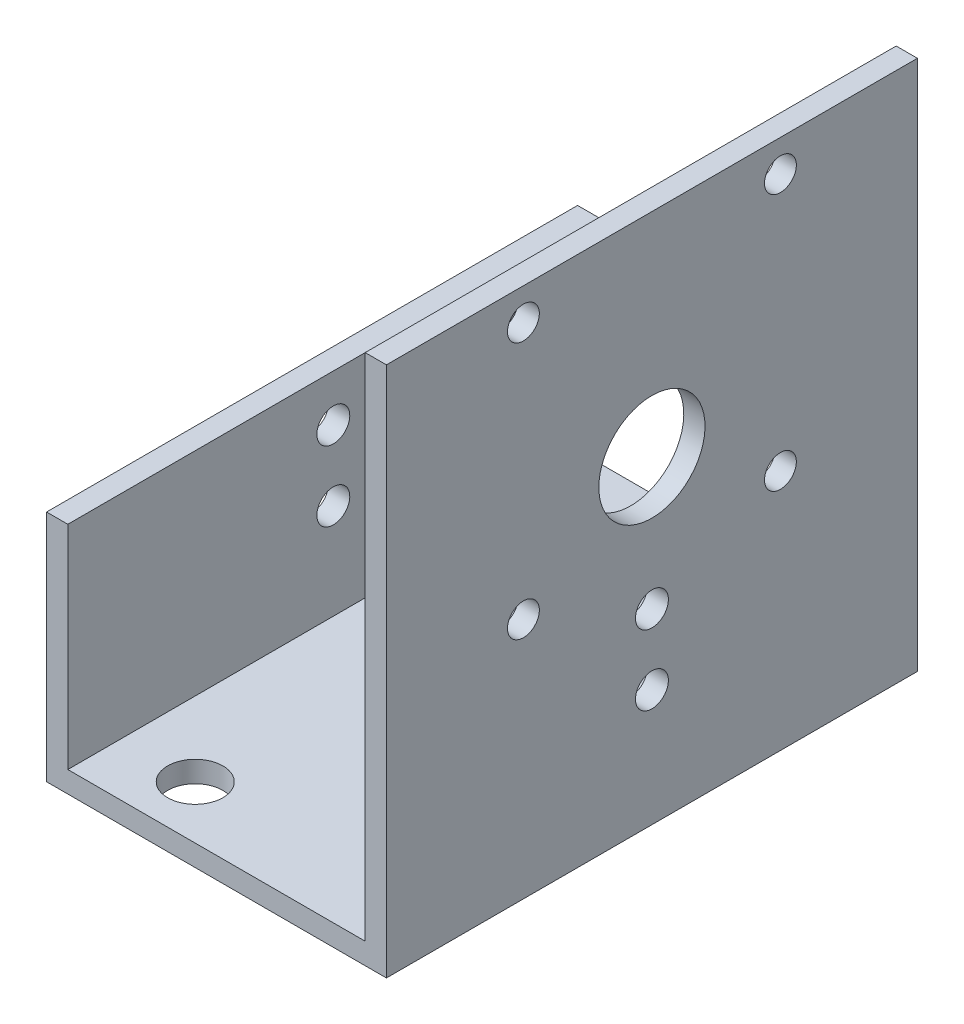
SolidWorks part; units mm, degrees
ref_plane "Plan de face" through (0, 0, 0) normal (0, 0, 1) x (1, 0, 0)
ref_plane "Plan de dessus" through (0, 0, 0) normal (0, 1, 0) x (1, 0, 0)
ref_plane "Plan de droite" through (0, 0, 0) normal (1, 0, 0) x (0, 0, -1)
sketch "Esquisse1" plane through (0, 0, 0) normal (0, 0, 1) x (1, 0, 0)
  line L0 (-28, -48) -> (-28, -50) construction
  line L1 (0, 0) -> (2, 0)
  line L2 (0, 0) -> (0, -48)
  line L4 (2, 0) -> (2, -50)
  line L5 (0, -48) -> (-28, -48)
  line L7 (2, -50) -> (-28, -50)
  line L9 (-28, -50) -> (-30, -50)
  line L10 (-28, -48) -> (-28, -28)
  line L11 (-28, -28) -> (-30, -28)
  line L12 (-30, -50) -> (-30, -28)
  dimension "D1" = 50
  dimension "D2" = 2
  dimension "D3" = 22
  dimension "D4" = 30
extrude "Extrusion1" add sketch "Esquisse1" along normal mid plane 50
sketch "Esquisse2" plane through (2, 0, 0) normal (1, 0, 0) x (0, 0, -1)
  line L0 (0, 0) -> (0, -20) construction
  line L1 (-25, 0) -> (25, 0) construction
  line L2 (-12.1, -3) -> (12.1, -3) construction
  line L3 (-12.1, -3) -> (-12.1, -27.2) construction
  line L4 (-12.1, -27.2) -> (12.1, -27.2) construction
  line L5 (12.1, -3) -> (12.1, -27.2) construction
  circle A0 centre (-12.1, -3) radius 1.5
  circle A1 centre (-12.1, -27.2) radius 1.5
  circle A2 centre (12.1, -27.2) radius 1.5
  circle A3 centre (12.1, -3) radius 1.5
  circle A4 centre (0, -20) radius 5
  dimension "D1" = 3
  dimension "D2" = 10
  dimension "D7" = 7.2
  dimension "D3" = 3
  dimension "D4" = 24.2
  dimension "D5" = 12.1
  dimension "D6" = 24.2
extrude "Enlèv. mat.-Extru.1" cut sketch "Esquisse2" against normal blind 10
sketch "Esquisse3" plane through (2, 0, 0) normal (1, 0, 0) x (0, 0, -1)
  line L0 (0, -50) -> (0, -39) construction
  line L1 (-25, -50) -> (25, -50) construction
  line L2 (0, -39) -> (0, -32.4) construction
  circle A0 centre (0, -32.4) radius 1.55
  circle A1 centre (0, -39) radius 1.55
  dimension "D2" = 3.1
  dimension "D3" = 11
  dimension "D1" = 17.6
extrude "Enlèv. mat.-Extru.2" cut sketch "Esquisse3" against normal through all
sketch "Esquisse4" plane through (0, -50, 0) normal (0, -1, 0) x (1, 0, 0)
  line L0 (-21, 20) -> (-21, -20) construction
  line L1 (-30, 25) -> (-30, -25) construction
  circle A0 centre (-21, 20) radius 2.6
  circle A1 centre (-21, -20) radius 2.6
  dimension "D1" = 20
  dimension "D2" = 5.2
  dimension "D3" = 9
  dimension "D4" = 40
extrude "Enlèv. mat.-Extru.3" cut sketch "Esquisse4" against normal blind 10
